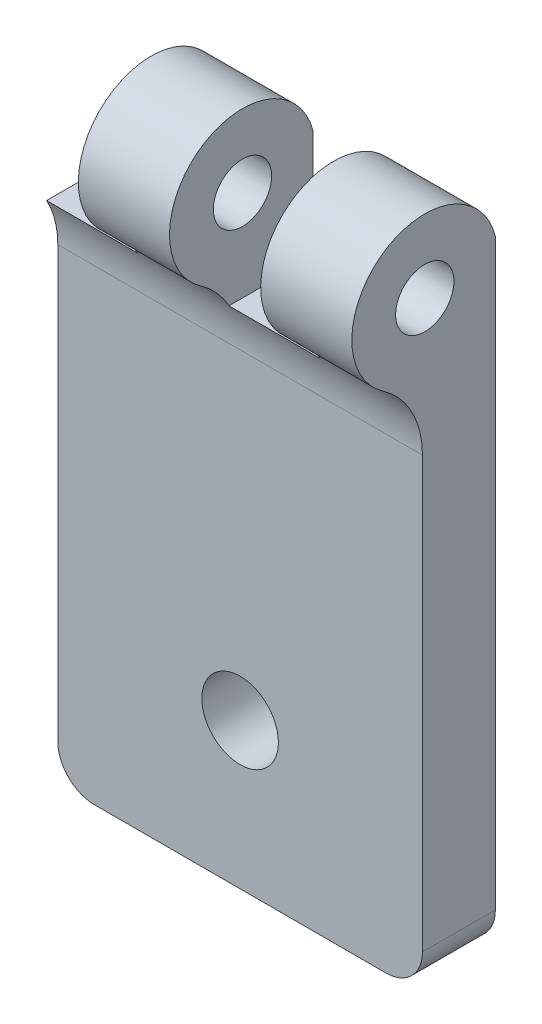
SolidWorks part; units mm, degrees
ref_plane "Front Plane" through (0, 0, 0) normal (0, 0, 1) x (1, 0, 0)
ref_plane "Top Plane" through (0, 0, 0) normal (0, 1, 0) x (1, 0, 0)
ref_plane "Right Plane" through (0, 0, 0) normal (1, 0, 0) x (0, 0, -1)
sketch "Sketch1" plane through (0, 0, 0) normal (0, 0, 1) x (1, 0, 0)
  line L1 (0, 0) -> (-20, 0)
  line L2 (0, 0) -> (0, 34)
  line L3 (0, 34) -> (-20, 34)
  line L4 (-20, 0) -> (-20, 34)
  dimension "D1" = 20
  dimension "D2" = 34
extrude "Boss-Extrude1" add sketch "Sketch1" along normal blind 4
sketch "Sketch2" plane through (0, 0, 0) normal (1, 0, 0) x (0, 0, -1)
  line L0 (-4, 0) -> (-4, 34) construction
  line L1 (-4, 29) -> (-4, 34)
  line L2 (-4, 34) -> (0, 34)
  arc A0 (0, 34) -> (-4, 29) centre (-3.8725, 32.998) ccw
  dimension "D2" = 4
  dimension "D1" = 5
extrude "Boss-Extrude2" add sketch "Sketch2" against normal up to surface (20 mm away) up to face at (-20, 17, 2)
fillet "Fillet1" radius 5 1 edges at (-10, 29, 4)
sketch "Sketch3" plane through (0, 0, 0) normal (1, 0, 0) x (0, 0, -1)
  circle A0 centre (-3.8725, 32.998) radius 1.6
  arc A1 (0, 34) -> (-6.1514, 29.7106) centre (-3.8725, 32.998) ccw construction
  dimension "D1" = 3.2
extrude "Cut-Extrude1" cut sketch "Sketch3" against normal through all
sketch "Sketch4" plane through (0, 0, 4) normal (0, 0, 1) x (1, 0, 0)
  line L0 (0, 0) -> (0, 25.6015) construction
  line L1 (-20, 0) -> (0, 0) construction
  circle A0 centre (-10, 8) radius 2.1
  dimension "D1" = 4.2
  dimension "D2" = 10
  dimension "D3" = 8
extrude "Cut-Extrude2" cut sketch "Sketch4" against normal through all
fillet "Fillet2" radius 2 2 edges at (0, 0, 2) (-20, 0, 2)
sketch "Sketch5" plane through (0, 0, 0) normal (0, 0, -1) x (-1, 0, 0)
  line L1 (5, 28) -> (10, 28)
  line L2 (5, 28) -> (5, 40)
  line L3 (5, 40) -> (10, 40)
  line L4 (10, 28) -> (10, 40)
  line L5 (18, 0) -> (2, 0) construction
  line L6 (15, 28) -> (20, 28)
  line L7 (15, 28) -> (15, 40)
  line L8 (15, 40) -> (20, 40)
  line L9 (20, 28) -> (20, 40)
  line L10 (20, 34) -> (20, 2) construction
  dimension "D1" = 5
  dimension "D2" = 5
  dimension "D3" = 5
  dimension "D4" = 28
  dimension "D5" = 28
  dimension "D6" = 12
  dimension "D7" = 12
extrude "Cut-Extrude3" cut sketch "Sketch5" against normal through all
